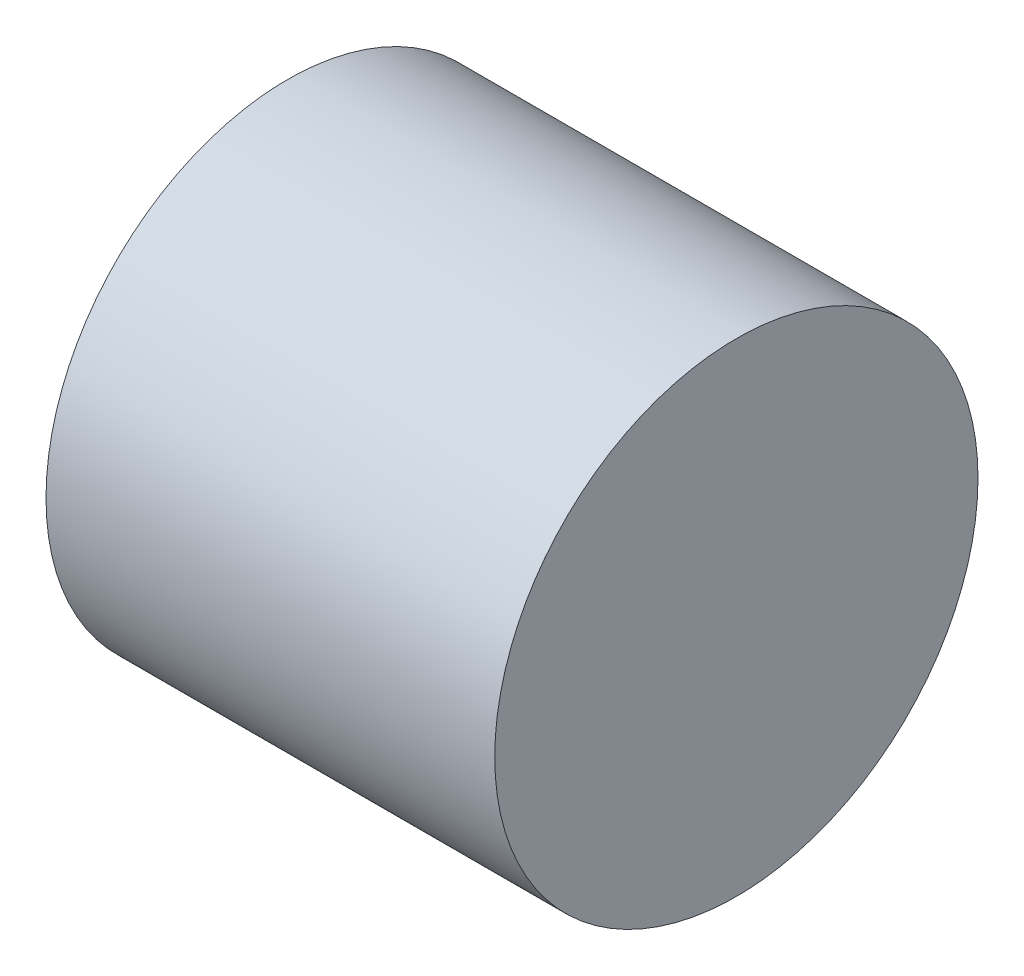
SolidWorks part; units mm, degrees
ref_plane "Front Plane" through (0, 0, 0) normal (0, 0, 1) x (1, 0, 0)
ref_plane "Top Plane" through (0, 0, 0) normal (0, 1, 0) x (1, 0, 0)
ref_plane "Right Plane" through (0, 0, 0) normal (1, 0, 0) x (0, 0, -1)
sketch "Sketch1" plane through (0, 0, 0) normal (1, 0, 0) x (0, 0, -1)
  circle A0 centre (0, 0) radius 7
  dimension "D1" = 14
extrude "Boss-Extrude1" add sketch "Sketch1" along normal blind 13
